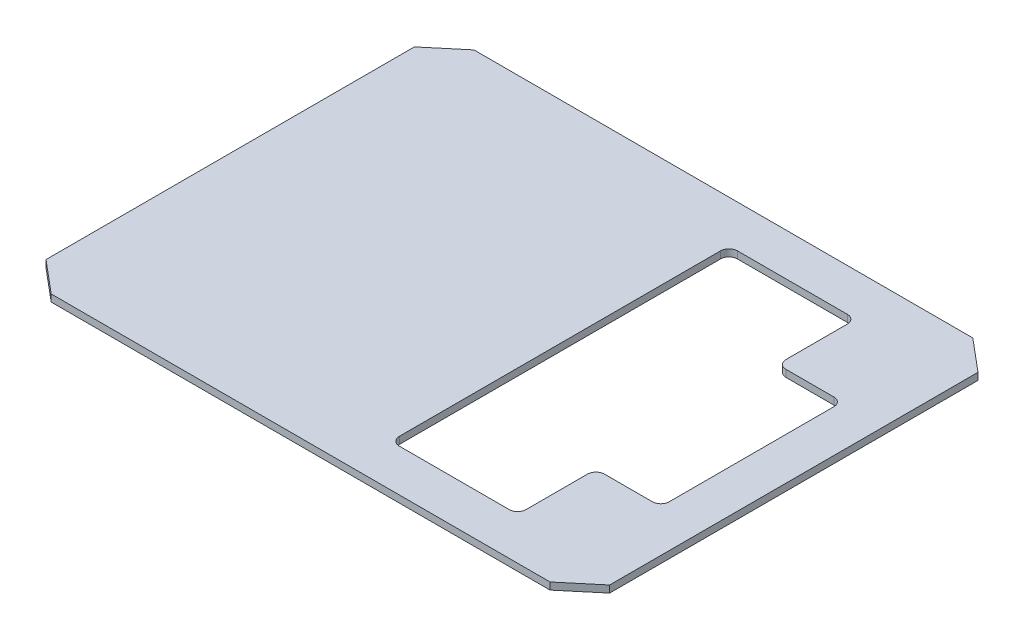
SolidWorks part; units mm, degrees
material "Thornel Mat VMA"
ref_plane "Front Plane" through (0, 0, 0) normal (0, 0, 1) x (1, 0, 0)
ref_plane "Top Plane" through (0, 0, 0) normal (0, 1, 0) x (1, 0, 0)
ref_plane "Right Plane" through (0, 0, 0) normal (1, 0, 0) x (0, 0, -1)
sketch "Sketch1" plane through (0, 0, 0) normal (0, 1, 0) x (1, 0, 0)
  line L0 (0, -95.25) -> (0, 95.25) construction
  line L1 (-127, 95.25) -> (127, 95.25) construction
  line L2 (-127, 95.25) -> (-127, -95.25) construction
  line L3 (-127, -95.25) -> (127, -95.25) construction
  line L4 (127, 95.25) -> (127, -95.25) construction
  line L5 (-127, 0) -> (127, 0) construction
  line L6 (-114.3, 0) -> (-114.3, 52.7344) construction
  line L7 (-114.3, 52.7344) -> (-101.6, 52.7344) construction
  line L8 (-101.6, 52.7344) -> (-87.0069, 64.9795) construction
  line L9 (-87.0069, 64.9795) -> (-87.0069, 76.2) construction
  line L10 (-87.0069, 76.2) -> (0, 76.2) construction
  line L11 (-127, 83.0049) -> (-112.4069, 95.25) construction
  line L12 (-87.0069, 64.9795) -> (-112.4069, 95.25) construction
  line L13 (-101.6, 52.7344) -> (-127, 83.0049) construction
  line L15 (-127, 95.25) -> (127, 95.25) construction
  line L16 (-127, 95.25) -> (-127, -95.25) construction
  line L17 (-127, -95.25) -> (127, -95.25) construction
  line L18 (127, 95.25) -> (127, -95.25) construction
  line L19 (-127, 95.25) -> (127, -95.25) construction
  line L20 (-127, -95.25) -> (127, 95.25) construction
  line L22 (127, -83.0049) -> (112.4069, -95.25)
  line L23 (-127, -83.0049) -> (-112.4069, -95.25)
  line L24 (-112.4069, 95.25) -> (112.4069, 95.25)
  line L25 (-127, -83.0049) -> (-127, 83.0049)
  line L26 (127, 83.0049) -> (127, -83.0049)
  line L27 (112.4069, -95.25) -> (-112.4069, -95.25)
  line L28 (-94.3034, 58.8569) -> (-119.7034, 89.1274) construction
  line L33 (-127, 83.0049) -> (-112.4069, 95.25)
  line L36 (127, 83.0049) -> (112.4069, 95.25)
  point P8 (0, 0)
  point P18 (0, 0)
  dimension "D1" = 190.5
  dimension "D2" = 254
  dimension "D3" = 12.7
  dimension "D4" = 19.05
  dimension "D5" = 12.7
  dimension "D6" = 40
  dimension "D7" = 19.05
  dimension "D8" = 0
  dimension "D9" = 12.7
extrude "Boss-Extrude1" add sketch "Sketch1" along normal blind 3.175
sketch "Sketch2" plane through (0, 3.175, 0) normal (0, 1, 0) x (1, 0, 0)
  line L0 (0, 0) -> (127, 0) construction
  line L1 (127, 83.0049) -> (127, -83.0049) construction
  line L2 (82.55, 40.894) -> (104.14, 40.894)
  line L3 (25.4, 76.2) -> (74.93, 76.2)
  line L4 (21.59, 72.39) -> (21.59, -72.39)
  line L5 (25.4, -76.2) -> (74.93, -76.2)
  line L6 (78.74, 72.39) -> (78.74, 44.704)
  line L7 (21.59, 76.2) -> (78.74, -76.2) construction
  line L8 (21.59, -76.2) -> (78.74, 76.2) construction
  line L9 (107.95, 37.084) -> (107.95, -37.084)
  line L10 (127, 83.0049) -> (127, -83.0049) construction
  line L11 (78.74, -44.704) -> (78.74, -72.39)
  line L12 (82.55, -40.894) -> (104.14, -40.894)
  arc A0 (104.14, 40.894) -> (107.95, 37.084) centre (104.14, 37.084) cw
  arc A1 (82.55, 40.894) -> (78.74, 44.704) centre (82.55, 44.704) cw
  arc A2 (104.14, -40.894) -> (107.95, -37.084) centre (104.14, -37.084) ccw
  arc A3 (82.55, -40.894) -> (78.74, -44.704) centre (82.55, -44.704) ccw
  arc A4 (74.93, -76.2) -> (78.74, -72.39) centre (74.93, -72.39) ccw
  arc A5 (21.59, -72.39) -> (25.4, -76.2) centre (25.4, -72.39) ccw
  arc A6 (25.4, 76.2) -> (21.59, 72.39) centre (25.4, 72.39) ccw
  arc A7 (74.93, 76.2) -> (78.74, 72.39) centre (74.93, 72.39) cw
  point P5 (50.165, 0)
  point P17 (107.95, 0)
  point P19 (107.95, 40.894)
  point P22 (78.74, 40.894)
  point P25 (107.95, -40.894)
  point P28 (78.74, -40.894)
  dimension "D6" = 3.81
  dimension "D1" = 57.15
  dimension "D2" = 152.4
  dimension "D3" = 48.26
  dimension "D4" = 40.894
  dimension "D5" = 19.05
extrude "Cut-Extrude1" cut sketch "Sketch2" against normal through all
